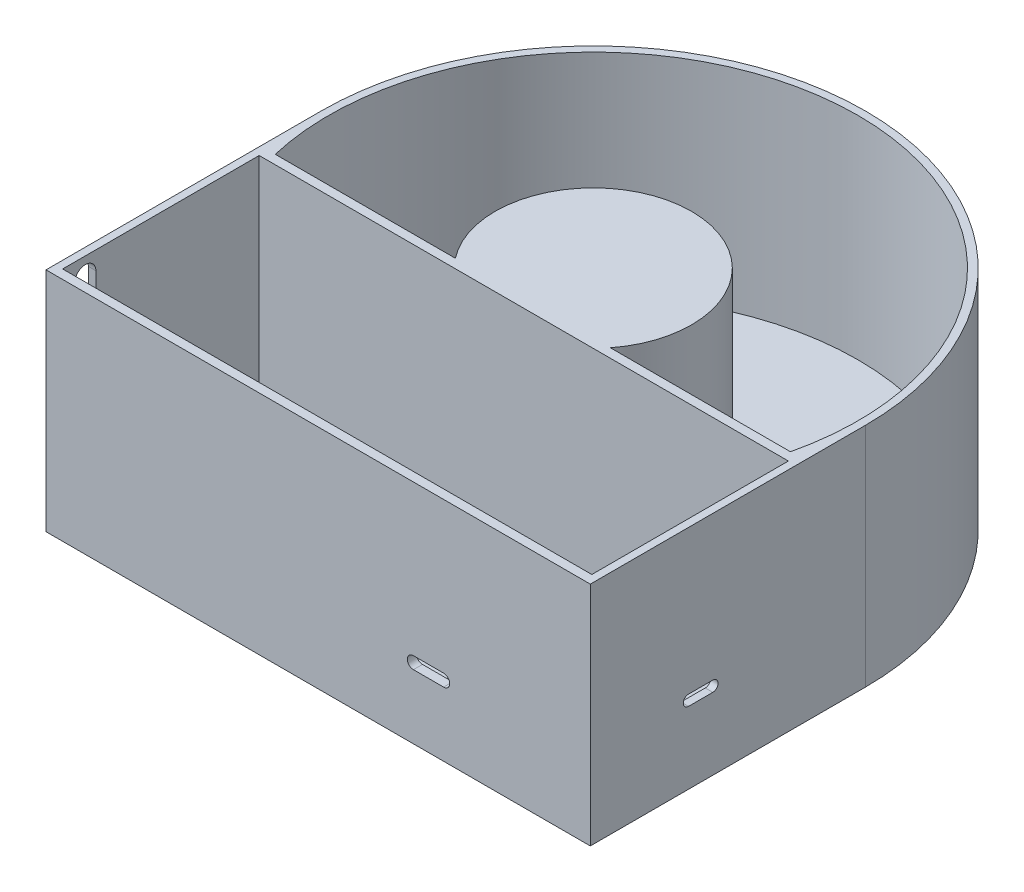
SolidWorks part; units mm, degrees
ref_plane "Front Plane" through (0, 0, 0) normal (0, 0, 1) x (1, 0, 0)
ref_plane "Top Plane" through (0, 0, 0) normal (0, 1, 0) x (1, 0, 0)
ref_plane "Right Plane" through (0, 0, 0) normal (1, 0, 0) x (0, 0, -1)
sketch "Sketch1" plane through (0, 0, 0) normal (0, 1, 0) x (1, 0, 0)
  circle A0 centre (0, 0) radius 90
  dimension "D1" = 180
extrude "Boss-Extrude1" add sketch "Sketch1" along normal blind 75
sketch "Sketch2" plane through (0, 75, 0) normal (0, 1, 0) x (1, 0, 0)
  circle A0 centre (0, 0) radius 87.5
  dimension "D1" = 175
extrude "Cut-Extrude1" cut sketch "Sketch2" against normal blind 70
sketch "Sketch3" plane through (0, 5, 0) normal (0, 1, 0) x (1, 0, 0)
  circle A0 centre (0, 0) radius 32.5
  dimension "D1" = 65
extrude "Boss-Extrude2" add sketch "Sketch3" along normal blind 70
sketch "Sketch4" plane through (0, 75, 0) normal (0, 1, 0) x (1, 0, 0)
  line L0 (123.5268, -32.5) -> (-123.5268, -32.5) construction
  line L1 (-90, 97.6897) -> (-90, -103.7846) construction
  line L2 (90, 100.5521) -> (90, -106.647) construction
  line L4 (-90, -32.5) -> (90, -32.5)
  line L5 (-90, -32.5) -> (-90, -98.5)
  line L6 (-90, -98.5) -> (90, -98.5)
  line L7 (90, -32.5) -> (90, -98.5)
  circle A0 centre (0, 0) radius 32.5 construction
  point P3 (0, -32.5)
  point P6 (-90, -3.0474)
  point P9 (90, -3.0474)
  dimension "D1" = 66
  dimension "D2" = 32.5
extrude "Cut-Extrude2" cut sketch "Sketch4" against normal blind 75
sketch "Sketch5" plane through (0, 75, 0) normal (0, 1, 0) x (1, 0, 0)
  line L1 (-87.7496, -20) -> (87.2504, -20)
  line L2 (-87.7496, -20) -> (-87.7496, -81.1875)
  line L3 (-87.7496, -81.1875) -> (87.2504, -81.1875)
  line L4 (87.2504, -20) -> (87.2504, -81.1875)
  arc A0 (83.9271, -32.5) -> (-83.9271, -32.5) centre (0, 0) ccw construction
  dimension "D1" = 175
  dimension "D2" = 20
extrude "Cut-Extrude3" cut sketch "Sketch5" against normal blind 75
sketch "Sketch6" plane through (0, 75, 0) normal (0, 1, 0) x (1, 0, 0)
  line L3 (-89.9995, -103.8119) -> (90, -103.8119)
  line L5 (-89.9995, -20) -> (90, -20)
  line L6 (-89.9995, -20) -> (-89.9995, -103.8119)
  line L8 (90, -20) -> (90, -103.8119)
extrude "Cut-Extrude4" cut sketch "Sketch6" against normal blind 75
sketch "Sketch8" plane through (0, 75, 0) normal (0, 1, 0) x (1, 0, 0)
  line L0 (0, 0) -> (0, -20) construction
  line L2 (25.6174, -20) -> (-25.6174, -20) construction
  line L3 (90, -20) -> (-90, -20) construction
  line L5 (-90, -20) -> (90, -20)
  line L6 (-90, -20) -> (-90, -91)
  line L7 (-90, -91) -> (90, -91)
  line L8 (90, -20) -> (90, -91)
  point P3 (-0.0078, -20)
  point P8 (0, -20)
  dimension "D1" = 180
  dimension "D2" = 0
  dimension "D3" = 71
extrude "Boss-Extrude5" add sketch "Sketch8" against normal blind 75
sketch "Sketch9" plane through (0, 75, 0) normal (0, 1, 0) x (1, 0, 0)
  line L0 (-90, -20) -> (-90, 0)
  line L1 (90, -20) -> (90, 0)
  line L2 (-87.7496, -20) -> (-90, -20) construction
  line L3 (-90, -20) -> (-90, -91) construction
  arc A0 (87.7496, -20) -> (-87.7496, -20) centre (0, 0) ccw construction
sketch "Sketch10" plane through (-90, 0, 0) normal (-1, 0, 0) x (0, 0, 1)
  line L0 (0, 75) -> (0, 0)
  line L1 (20, 75) -> (0, 75) construction
  line L2 (20, 75) -> (-32.5, 75) construction
  line L3 (0, 0) -> (20, 0)
  line L4 (20, 0) -> (20, 75)
  line L5 (20, 75) -> (0, 75)
extrude "Boss-Extrude6" add sketch "Sketch10" against normal up to surface (2.2504 mm away)
sketch "Sketch11" plane through (90, 0, 0) normal (1, 0, 0) x (0, 0, -1)
  line L0 (0, 75) -> (0, 0)
  line L1 (-20, 75) -> (0, 75) construction
  line L2 (0, 0) -> (-20, 0)
  line L3 (-20, 0) -> (-20, 75)
  line L4 (-20, 75) -> (0, 75)
extrude "Boss-Extrude7" add sketch "Sketch11" against normal up to surface (2.2504 mm away)
sketch "Sketch12" plane through (0, 75, 0) normal (0, 1, 0) x (1, 0, 0)
  line L0 (-90, -20) -> (90, -20) construction
  line L1 (0, -20) -> (0, -91) construction
  line L2 (-90, -91) -> (90, -91) construction
  line L4 (87.5, -23) -> (-87.5, -23)
  line L5 (87.5, -23) -> (87.5, -88)
  line L6 (87.5, -88) -> (-87.5, -88)
  line L7 (-87.5, -23) -> (-87.5, -88)
  line L8 (87.5, -23) -> (-87.5, -88) construction
  line L9 (87.5, -88) -> (-87.5, -23) construction
  point P8 (0, -55.5)
  dimension "D1" = 65
  dimension "D2" = 175
extrude "Cut-Extrude5" cut sketch "Sketch12" against normal blind 70
sketch "Sketch13" plane through (87.5, 0, 0) normal (-1, 0, 0) x (0, 0, 1)
  line L0 (50.5, 25.5) -> (58.5, 25.5) construction
  line L1 (50.5, 27.25) -> (58.5, 27.25)
  line L2 (50.5, 23.75) -> (58.5, 23.75)
  line L3 (88, 5) -> (23, 5) construction
  line L4 (88, 5) -> (88, 75) construction
  arc A0 (50.5, 27.25) -> (50.5, 23.75) centre (50.5, 25.5) ccw
  arc A1 (58.5, 23.75) -> (58.5, 27.25) centre (58.5, 25.5) ccw
  point P2 (54.5, 25.5)
  dimension "D1" = 20.5
  dimension "D2" = 33.5
  dimension "D3" = 8
  dimension "D4" = 3.5
extrude "Cut-Extrude6" cut sketch "Sketch13" against normal blind 70
sketch "Sketch14" plane through (0, 0, 91) normal (0, 0, 1) x (1, 0, 0)
  line L0 (90, 37.5) -> (41.5, 37.5) construction
  line L1 (90, 0) -> (90, 75) construction
  line L2 (41.5, 75) -> (41.5, 23.25) construction
  line L3 (-90, 75) -> (90, 75) construction
  line L4 (41.5, 23.25) -> (31.5, 23.25) construction
  line L5 (41.5, 21.25) -> (31.5, 21.25)
  line L6 (41.5, 25.25) -> (31.5, 25.25)
  arc A0 (41.5, 21.25) -> (41.5, 25.25) centre (41.5, 23.25) ccw
  arc A1 (31.5, 25.25) -> (31.5, 21.25) centre (31.5, 23.25) ccw
  point P8 (36.5, 23.25)
  dimension "D1" = 48.5
  dimension "D2" = 51.75
  dimension "D3" = 10
  dimension "D4" = 4
extrude "Cut-Extrude7" cut sketch "Sketch14" against normal blind 10
sketch "Sketch15" plane through (0, 0, 20) normal (0, 0, -1) x (-1, 0, 0)
  line L0 (55.4005, 5) -> (57.1212, 7.4575)
  line L1 (25.6174, 5) -> (85.1836, 5) construction
  line L2 (57.1212, 7.4575) -> (56.1212, 7.4575)
  line L3 (56.1212, 7.4575) -> (54.4005, 5)
  line L4 (55.4005, 5) -> (75.4005, 5) construction
  line L5 (65.4005, 5) -> (65.4005, 22.2692) construction
  line L6 (54.4005, 5) -> (55.4005, 5)
  line L7 (73.6798, 7.4575) -> (74.6798, 7.4575)
  line L8 (75.4005, 5) -> (73.6798, 7.4575)
  line L9 (76.4005, 5) -> (75.4005, 5)
  line L10 (74.6798, 7.4575) -> (76.4005, 5)
  dimension "D1" = 125
  dimension "D2" = 1
  dimension "D3" = 1
  dimension "D4" = 3
  dimension "D5" = 20
extrude "Boss-Extrude8" add sketch "Sketch15" along normal blind 50
sketch "Sketch17" plane through (-90, 0, 0) normal (-1, 0, 0) x (0, 0, 1)
  line L0 (80.5, 69) -> (80.5, 54) construction
  line L1 (84, 69) -> (84, 54)
  line L2 (77, 69) -> (77, 54)
  line L3 (91, 0) -> (91, 75) construction
  line L4 (0, 75) -> (91, 75) construction
  arc A0 (84, 69) -> (77, 69) centre (80.5, 69) ccw
  arc A1 (77, 54) -> (84, 54) centre (80.5, 54) ccw
  point P2 (80.5, 61.5)
  dimension "D3" = 6
  dimension "D1" = 7
  dimension "D2" = 7
  dimension "D4" = 15
extrude "Cut-Extrude8" cut sketch "Sketch17" against normal blind 50
